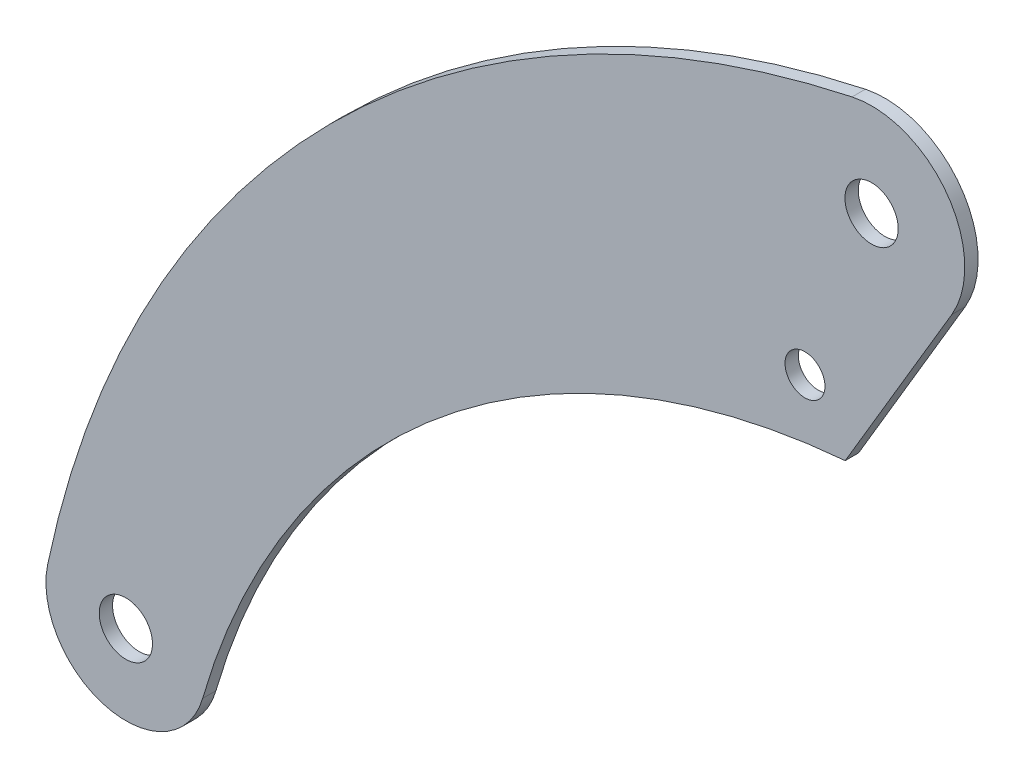
SolidWorks part; units mm, degrees
ref_plane "Front Plane" through (0, 0, 0) normal (0, 0, 1) x (1, 0, 0)
ref_plane "Top Plane" through (0, 0, 0) normal (0, 1, 0) x (1, 0, 0)
ref_plane "Right Plane" through (0, 0, 0) normal (1, 0, 0) x (0, 0, -1)
sketch "Sketch2" plane through (0, 0, 0) normal (0, 0, 1) x (1, 0, 0)
  line L0 (620.2204, 514.3138) -> (540.2204, 379.3138)
  circle A0 centre (0, 0) radius 20
  arc A3 (57.6581, -16.5995) -> (-58.7157, 12.3476) centre (0, 0) cw
  circle A4 centre (560, 550) radius 20
  arc A5 (620.2204, 514.3138) -> (545.3654, 618.4531) centre (560, 550) ccw
  arc A6 (540.2204, 379.3138) -> (57.6581, -16.5995) centre (586.1907, -168.7616) ccw
  arc A7 (545.3654, 618.4531) -> (-58.7157, 12.3476) centre (709.4818, -149.1997) ccw
  circle A8 centre (510, 420) radius 15
  dimension "D1" = 40
  dimension "D2" = 60
  dimension "D5" = 40
  dimension "D6" = 140
  dimension "D9" = 1100
  dimension "D10" = 1570
  dimension "D13" = 30
  dimension "D3" = 560
  dimension "D4" = 550
  dimension "D7" = 135
  dimension "D8" = 80
  dimension "D11" = 130
  dimension "D12" = 50
extrude "Boss-Extrude1" add sketch "Sketch2" along normal mid plane 10
